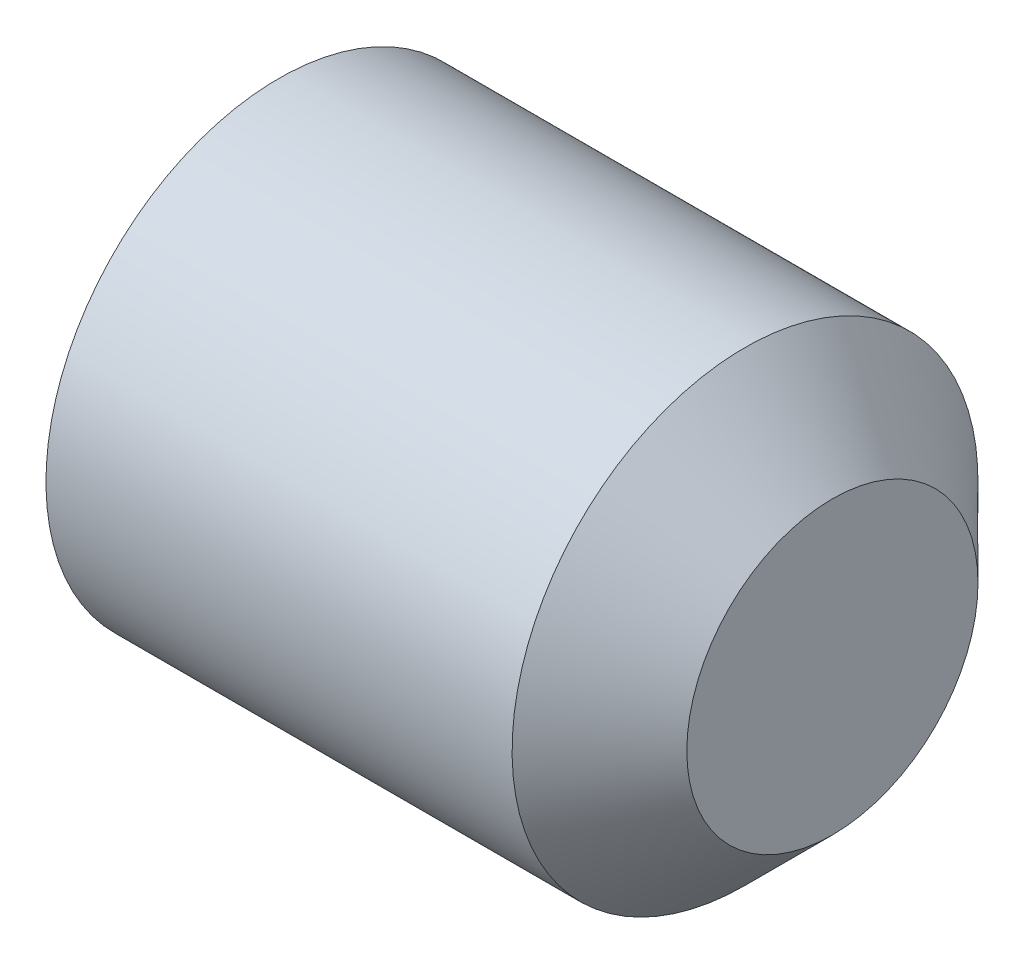
SolidWorks part; units mm, degrees
ref_plane "Front Plane" through (0, 0, 0) normal (0, 0, 1) x (1, 0, 0)
ref_plane "Top Plane" through (0, 0, 0) normal (0, 1, 0) x (1, 0, 0)
ref_plane "Right Plane" through (0, 0, 0) normal (1, 0, 0) x (0, 0, -1)
ref_plane "Plane1" through (0, 0, 0) normal (0, 0, 1) x (1, 0, 0)
sketch "Sketch1" plane through (0, 0, 0) normal (0, 0, 1) x (1, 0, 0)
  line L0 (5, 0) -> (5, -1.25)
  line L1 (5, -1.25) -> (4.25, -2)
  line L2 (4.25, -2) -> (0.248, -2)
  line L3 (0.248, -2) -> (0, -1.5705)
  line L4 (0, -1.5705) -> (0, -1.1547)
  line L5 (0, -1.1547) -> (0.6667, 0)
  line L6 (0.6667, 0) -> (5, 0)
  line L7 (0.6667, 0) -> (5, 0) construction
revolve "Revolve1" add sketch "Sketch1" angle 360 about L7
ref_plane "Plane2" through (0, 0, 0) normal (1, 0, 0) x (0, 0, -1)
sketch "Sketch2" plane through (0, 0, 0) normal (1, 0, 0) x (0, 0, -1)
  line L0 (-1.1547, 0) -> (-0.5774, -1)
  line L1 (-0.5774, -1) -> (0.5774, -1)
  line L2 (0.5774, -1) -> (1.1547, 0)
  line L3 (1.1547, 0) -> (0.5774, 1)
  line L4 (0.5774, 1) -> (-0.5774, 1)
  line L5 (-0.5774, 1) -> (-1.1547, 0)
extrude "Cut-Extrude1" cut sketch "Sketch2" along normal blind 1.5
